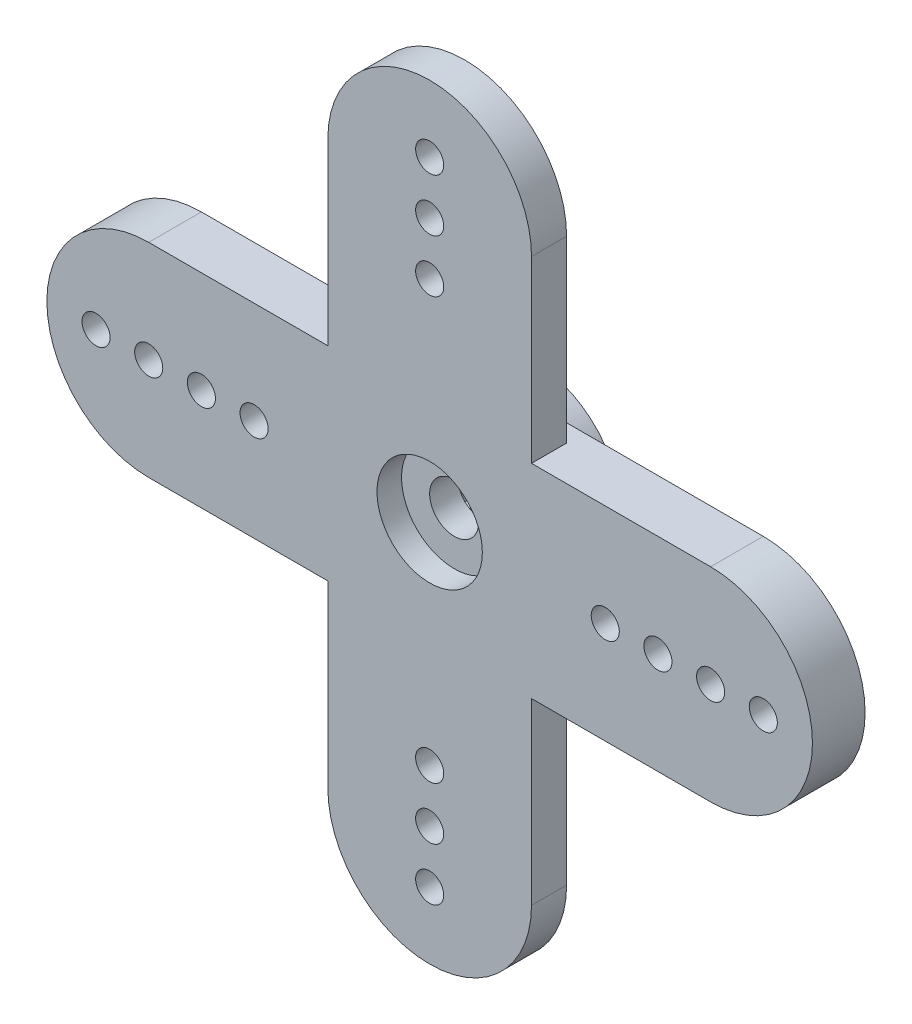
SolidWorks part; units mm, degrees
ref_plane "Face" through (0, 0, 0) normal (0, 0, 1) x (1, 0, 0)
ref_plane "Dessus" through (0, 0, 0) normal (0, 1, 0) x (1, 0, 0)
ref_plane "Droite" through (0, 0, 0) normal (1, 0, 0) x (0, 0, -1)
sketch "Esquisse1" plane through (0, 0, 0) normal (0, 0, 1) x (1, 0, 0)
  circle A0 centre (0, 0) radius 5
  line B0 (2.0116, -1.5509) -> (2.0116, -2.0116)
  line B1 (0.3258, 2.519) -> (0, 2.8448)
  line B2 (0.3373, 2.5175) -> (0.3258, 2.519)
  line B3 (0.7363, 2.7479) -> (0.3373, 2.5175)
  line B4 (0.9666, 2.3489) -> (0.7363, 2.7479)
  line B5 (0.9774, 2.3444) -> (0.9666, 2.3489)
  line B6 (1.4224, 2.4637) -> (0.9774, 2.3444)
  line B7 (1.5416, 2.0186) -> (1.4224, 2.4637)
  line B8 (1.5509, 2.0116) -> (1.5416, 2.0186)
  line B9 (2.0116, 2.0116) -> (1.5509, 2.0116)
  line B10 (2.0116, 1.5509) -> (2.0116, 2.0116)
  line B11 (2.0186, 1.5416) -> (2.0116, 1.5509)
  line B12 (2.4637, 1.4224) -> (2.0186, 1.5416)
  line B13 (2.3444, 0.9774) -> (2.4637, 1.4224)
  line B14 (2.3489, 0.9666) -> (2.3444, 0.9774)
  line B15 (2.7479, 0.7363) -> (2.3489, 0.9666)
  line B16 (2.5175, 0.3373) -> (2.7479, 0.7363)
  line B17 (2.519, 0.3258) -> (2.5175, 0.3373)
  line B18 (2.8448, 0) -> (2.519, 0.3258)
  line B19 (2.519, -0.3258) -> (2.8448, 0)
  line B20 (2.5175, -0.3373) -> (2.519, -0.3258)
  line B21 (2.7479, -0.7363) -> (2.5175, -0.3373)
  line B22 (2.3489, -0.9666) -> (2.7479, -0.7363)
  line B23 (2.3444, -0.9774) -> (2.3489, -0.9666)
  line B24 (2.4637, -1.4224) -> (2.3444, -0.9774)
  line B25 (2.0186, -1.5416) -> (2.4637, -1.4224)
  line B26 (2.0116, -1.5509) -> (2.0186, -1.5416)
  line B27 (1.5509, -2.0116) -> (2.0116, -2.0116)
  line B28 (1.5416, -2.0186) -> (1.5509, -2.0116)
  line B29 (1.4224, -2.4637) -> (1.5416, -2.0186)
  line B30 (0.9774, -2.3444) -> (1.4224, -2.4637)
  line B31 (0.9666, -2.3489) -> (0.9774, -2.3444)
  line B32 (0.7363, -2.7479) -> (0.9666, -2.3489)
  line B33 (0.3373, -2.5175) -> (0.7363, -2.7479)
  line B34 (0.3258, -2.519) -> (0.3373, -2.5175)
  line B35 (0, -2.8448) -> (0.3258, -2.519)
  line B36 (-0.3258, -2.519) -> (0, -2.8448)
  line B37 (-0.3373, -2.5175) -> (-0.3258, -2.519)
  line B38 (-0.7363, -2.7479) -> (-0.3373, -2.5175)
  line B39 (-0.9666, -2.3489) -> (-0.7363, -2.7479)
  line B40 (-0.9774, -2.3444) -> (-0.9666, -2.3489)
  line B41 (-1.4224, -2.4637) -> (-0.9774, -2.3444)
  line B42 (-1.5416, -2.0186) -> (-1.4224, -2.4637)
  line B43 (-1.5509, -2.0116) -> (-1.5416, -2.0186)
  line B44 (-2.0116, -2.0116) -> (-1.5509, -2.0116)
  line B45 (-2.0116, -1.5509) -> (-2.0116, -2.0116)
  line B46 (-2.0186, -1.5416) -> (-2.0116, -1.5509)
  line B47 (-2.4637, -1.4224) -> (-2.0186, -1.5416)
  line B48 (-2.3444, -0.9774) -> (-2.4637, -1.4224)
  line B49 (-2.3489, -0.9666) -> (-2.3444, -0.9774)
  line B50 (-2.7479, -0.7363) -> (-2.3489, -0.9666)
  line B51 (-2.5175, -0.3373) -> (-2.7479, -0.7363)
  line B52 (-2.519, -0.3258) -> (-2.5175, -0.3373)
  line B53 (-2.8448, 0) -> (-2.519, -0.3258)
  line B54 (-2.519, 0.3258) -> (-2.8448, 0)
  line B55 (-2.5175, 0.3373) -> (-2.519, 0.3258)
  line B56 (-2.7479, 0.7363) -> (-2.5175, 0.3373)
  line B57 (-2.3489, 0.9666) -> (-2.7479, 0.7363)
  line B58 (-2.3444, 0.9774) -> (-2.3489, 0.9666)
  line B59 (-2.4637, 1.4224) -> (-2.3444, 0.9774)
  line B60 (-2.0186, 1.5416) -> (-2.4637, 1.4224)
  line B61 (-2.0116, 1.5509) -> (-2.0186, 1.5416)
  line B62 (-2.0116, 2.0116) -> (-2.0116, 1.5509)
  line B63 (-1.5509, 2.0116) -> (-2.0116, 2.0116)
  line B64 (-1.5416, 2.0186) -> (-1.5509, 2.0116)
  line B65 (-1.4224, 2.4637) -> (-1.5416, 2.0186)
  line B66 (-0.9774, 2.3444) -> (-1.4224, 2.4637)
  line B67 (-0.9666, 2.3489) -> (-0.9774, 2.3444)
  line B68 (-0.7363, 2.7479) -> (-0.9666, 2.3489)
  line B69 (-0.3373, 2.5175) -> (-0.7363, 2.7479)
  line B70 (-0.3258, 2.519) -> (-0.3373, 2.5175)
  line B71 (0, 2.8448) -> (-0.3258, 2.519)
  dimension "D1" = 10
sketch_block_instance "Block1-1"
sketch_block "Block1"
extrude "Boss.-Extru.1" add sketch "Esquisse1" along normal blind 2.9
sketch "Esquisse2" plane through (0, 0, 2.9) normal (0, 0, 1) x (1, 0, 0)
  line L0 (-16, 0) -> (16, 0) construction
  line L1 (-16, 5.8) -> (16, 5.8)
  line L2 (-16, -5.8) -> (16, -5.8)
  arc A0 (-16, 5.8) -> (-16, -5.8) centre (-16, 0) ccw
  arc A1 (16, -5.8) -> (16, 5.8) centre (16, 0) ccw
  point P2 (0, 0)
  dimension "D1" = 5.8
  dimension "D2" = 32
extrude "Boss.-Extru.2" add sketch "Esquisse2" along normal blind 3
sketch "Esquisse3" plane through (0, 0, 5.9) normal (0, 0, 1) x (1, 0, 0)
  line L0 (0, 16) -> (0, -16) construction
  line L1 (5.8, 16) -> (5.8, -16)
  line L2 (-5.8, 16) -> (-5.8, -16)
  arc A0 (5.8, 16) -> (-5.8, 16) centre (0, 16) ccw
  arc A1 (-5.8, -16) -> (5.8, -16) centre (0, -16) ccw
  point P2 (0, 0)
  dimension "D1" = 5.8
  dimension "D2" = 32
extrude "Boss.-Extru.3" add sketch "Esquisse3" against normal blind 2
sketch "Esquisse4" plane through (0, 0, 5.9) normal (0, 0, 1) x (1, 0, 0)
  line L0 (0, 0) -> (-21.8, 0) construction
  circle A0 centre (-10, 0) radius 0.8
  circle A1 centre (-13, 0) radius 0.8
  circle A2 centre (-16, 0) radius 0.8
  circle A3 centre (-19, 0) radius 0.8
  arc A4 (-16, 5.8) -> (-16, -5.8) centre (-16, 0) ccw construction
  dimension "D5" = 1.6
  dimension "D1" = 10
  dimension "D2" = 13
  dimension "D3" = 16
  dimension "D4" = 19
extrude "Enlèv. mat.-Extru.1" cut sketch "Esquisse4" against normal through all
sketch "Esquisse5" plane through (0, 0, 5.9) normal (0, 0, 1) x (1, 0, 0)
  line L0 (0, 0) -> (0, 21.8) construction
  arc A0 (5.8, 16) -> (-5.8, 16) centre (0, 16) ccw construction
  circle A1 centre (0, 12) radius 0.8
  circle A2 centre (0, 15) radius 0.8
  circle A3 centre (0, 18) radius 0.8
  dimension "D1" = 1.6
  dimension "D2" = 12
  dimension "D3" = 15
  dimension "D4" = 18
extrude "Enlèv. mat.-Extru.2" cut sketch "Esquisse5" against normal through all
pattern_circular "Répétition circulaire1" count 2 over 360 about axis through (0, 0, 0) along (0, 0, 1) of "Enlèv. mat.-Extru.1", "Enlèv. mat.-Extru.2"
sketch "Esquisse6" plane through (0, 0, 5.9) normal (0, 0, 1) x (1, 0, 0)
  circle A0 centre (0, 0) radius 3
  dimension "D1" = 6
extrude "Enlèv. mat.-Extru.3" cut sketch "Esquisse6" against normal blind 1.4
sketch "Esquisse7" plane through (0, 0, 4.5) normal (0, 0, 1) x (1, 0, 0)
  circle A0 centre (0, 0) radius 1.4
  dimension "D1" = 2.8
extrude "Enlèv. mat.-Extru.4" cut sketch "Esquisse7" against normal through all
equation "\"D1@Esquisse5\"=\"D5@Esquisse4\""
